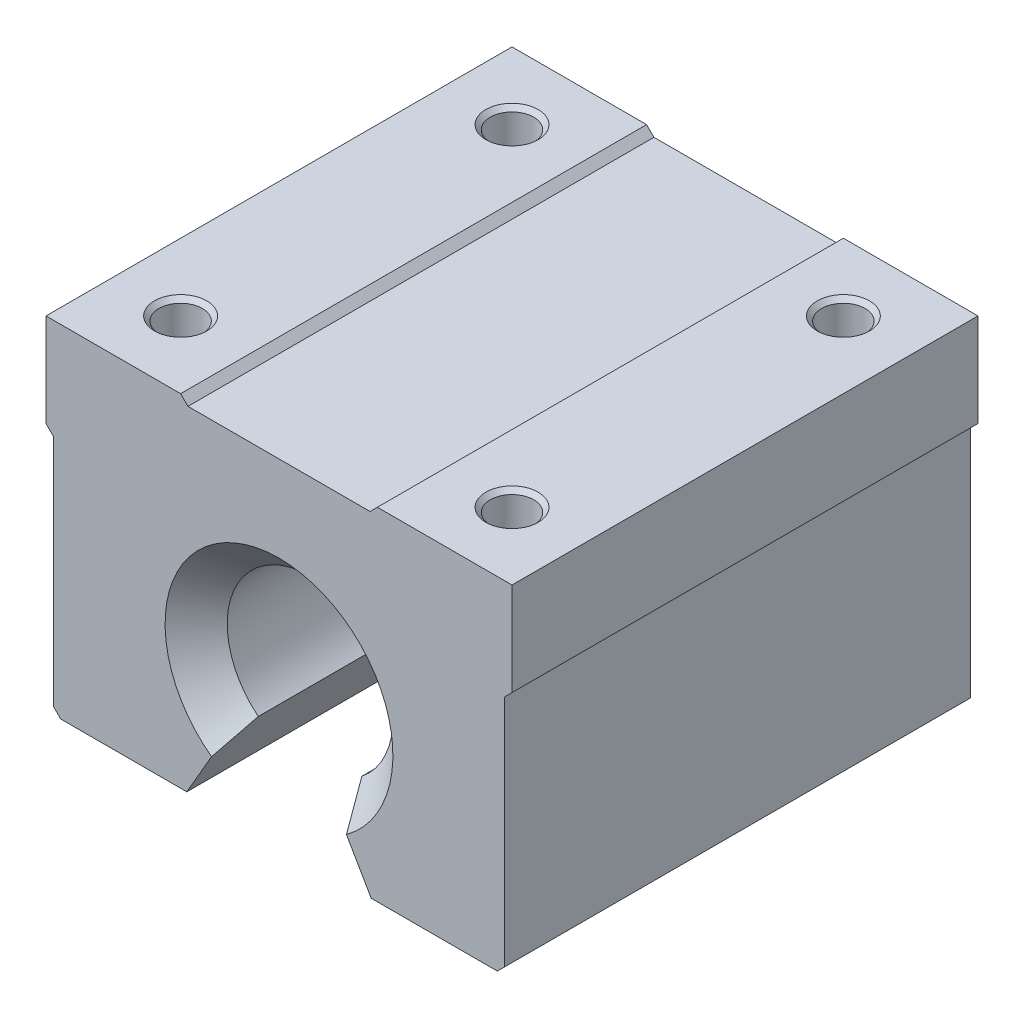
SolidWorks part; units mm, degrees
ref_plane "Front Plane" through (0, 0, 0) normal (0, 0, 1) x (1, 0, 0)
ref_plane "Top Plane" through (0, 0, 0) normal (0, 1, 0) x (1, 0, 0)
ref_plane "Right Plane" through (0, 0, 0) normal (1, 0, 0) x (0, 0, -1)
sketch "Sketch1" plane through (0, 0, 0) normal (0, 0, 1) x (1, 0, 0)
  line L0 (-22.5, 20) -> (-22.5, 11)
  line L5 (-22.5, 11) -> (-21.7929, 10.2929)
  line L6 (-21.7929, 10.2929) -> (-21.7929, -12.2929)
  line L7 (-21.7929, -12.2929) -> (-21.0858, -13)
  line L8 (-21.0858, -13) -> (-8.9, -13)
  line L9 (-8.9, -13) -> (-5, -6.245)
  line L10 (-22.5, 20) -> (-9.5, 20)
  line L11 (-9.5, 20) -> (-8.7929, 19.2929)
  line L12 (-8.7929, 19.2929) -> (8.7929, 19.2929)
  line L13 (0, 0) -> (0, 19.2929) construction
  line L14 (8.9, -13) -> (5, -6.245)
  line L15 (21.0858, -13) -> (8.9, -13)
  line L16 (21.7929, -12.2929) -> (21.0858, -13)
  line L17 (21.7929, 10.2929) -> (21.7929, -12.2929)
  line L18 (22.5, 11) -> (21.7929, 10.2929)
  line L19 (22.5, 20) -> (22.5, 11)
  line L20 (22.5, 20) -> (9.5, 20)
  line L21 (9.5, 20) -> (8.7929, 19.2929)
  arc A0 (5, -6.245) -> (-5, -6.245) centre (0, 0) ccw
  dimension "D2" = 16
  dimension "D1" = 45
  dimension "D3" = 33
  dimension "D4" = 60
  dimension "D5" = 135
  dimension "D6" = 9
  dimension "D7" = 10
  dimension "D8" = 1
  dimension "D9" = 20
  dimension "D10" = 13
extrude "Boss-Extrude1" add sketch "Sketch1" along normal mid plane 45
sketch "Sketch2" plane through (0, 20, 0) normal (0, 1, 0) x (1, 0, 0)
  line L1 (-16, -16) -> (16, -16) construction
  line L2 (-16, -16) -> (-16, 16) construction
  line L3 (-16, 16) -> (16, 16) construction
  line L4 (16, -16) -> (16, 16) construction
  line L5 (-16, -16) -> (16, 16) construction
  line L6 (-16, 16) -> (16, -16) construction
  point P0 (0, 0)
  point P6 (0, 0)
  point P7 (-16, 16)
  point P8 (-16, -16)
  point P9 (16, -16)
  point P10 (16, 16)
  dimension "D1" = 32
hole_wizard "M5x0.8 Tapped Hole1" positions "3DSketch1" profile "Sketch3" tap size "M5x0.8" standard "ANSI Metric"
sketch3d "3DSketch1"
  point P0 (16, 20, 16)
  point P3 (16, 20, -16)
  point P6 (-16, 20, -16)
  point P9 (-16, 20, 16)
sketch "Sketch3" plane through (16, 20, 16) normal (1, 0, 0) x (0, 0, 1)
  line L0 (0, 0) -> (0, 13.2618)
  line L1 (0, 13.2618) -> (2.1, 12)
  line L2 (2.1, 12) -> (2.1, 0.425)
  line L3 (2.1, 0.425) -> (2.525, 0)
  line L5 (2.525, 0) -> (0, 0)
  line L6 (-2.1, 0.425) -> (-2.525, 0) construction
  line L10 (0, 13.2618) -> (-2.1, 12) construction
  line L11 (0, -6.35) -> (0, 107.95) construction
  dimension "Tap Drill Dia." = 4.2
  dimension "Tap Drill Depth" = 12
  dimension "Near C'Sink Dia." = 5.05
  dimension "Near C'Sink Angle" = 90
  dimension "Drill Angle" = 118
cosmetic thread "Hole Thread1" parameters "D1"=9.906, "D2"=5
cosmetic thread "Hole Thread2" parameters "D1"=9.906, "D2"=5
cosmetic thread "Hole Thread3" parameters "D1"=9.906, "D2"=5
cosmetic thread "Hole Thread4" parameters "D1"=9.906, "D2"=5
chamfer "Chamfer1" distance 3 angle 45 2 edges at (0, 8, -22.5) (0, 8, 22.5)
